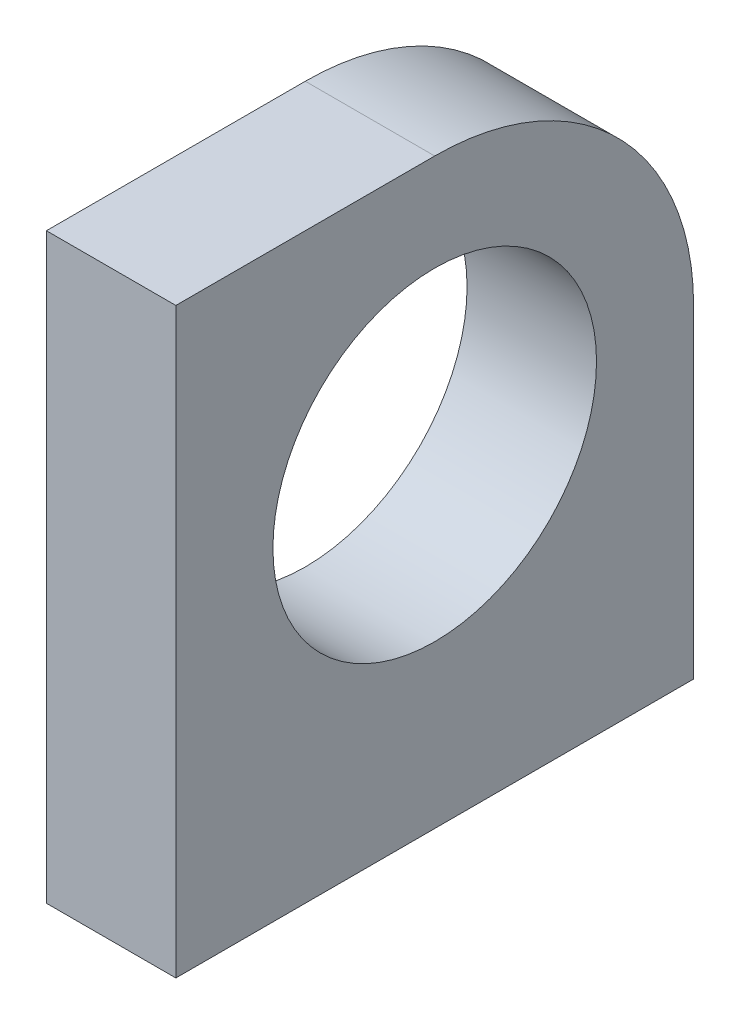
SolidWorks part; units mm, degrees
ref_plane "Front Plane" through (0, 0, 0) normal (0, 0, 1) x (1, 0, 0)
ref_plane "Top Plane" through (0, 0, 0) normal (0, 1, 0) x (1, 0, 0)
ref_plane "Right Plane" through (0, 0, 0) normal (1, 0, 0) x (0, 0, -1)
sketch "Sketch1" plane through (0, 0, 0) normal (1, 0, 0) x (0, 0, -1)
  line L1 (-25.4, 28.575) -> (25.4, 28.575)
  line L2 (-25.4, 28.575) -> (-25.4, -28.575)
  line L3 (-25.4, -28.575) -> (25.4, -28.575)
  line L4 (25.4, 28.575) -> (25.4, -28.575)
  line L5 (-25.4, 28.575) -> (25.4, -28.575) construction
  line L6 (-25.4, -28.575) -> (25.4, 28.575) construction
  point P0 (0, 0)
  dimension "D1" = 50.8
  dimension "D2" = 57.15
extrude "Boss-Extrude1" add sketch "Sketch1" along normal mid plane 12.7
sketch "Sketch2" plane through (6.35, 0, 0) normal (1, 0, 0) x (0, 0, -1)
  line L0 (0, 3.175) -> (0, -28.575) construction
  line L1 (-25.4, -28.575) -> (25.4, -28.575) construction
  circle A0 centre (0, 3.175) radius 15.875
  dimension "D1" = 31.75
  dimension "D2" = 31.75
extrude "Cut-Extrude1" cut sketch "Sketch2" against normal up to next
fillet "Fillet1" radius 25.4 1 edges at (0, 28.575, -25.4)
